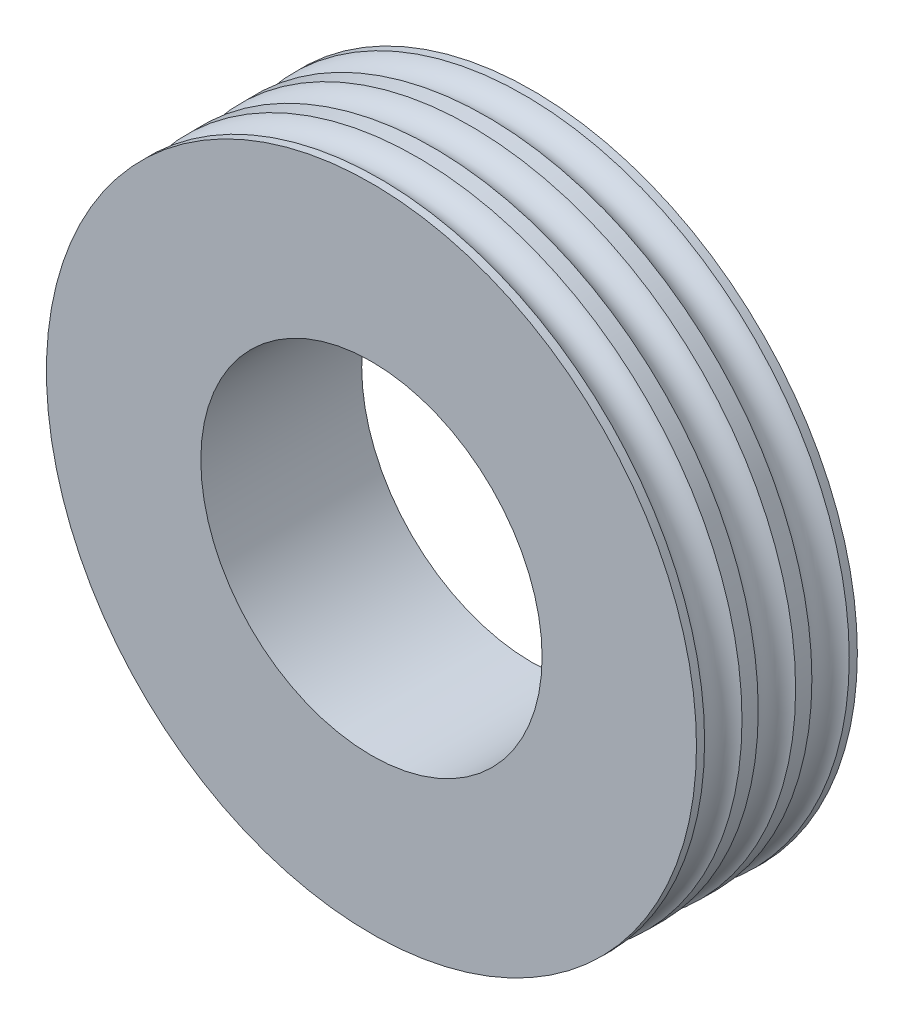
SolidWorks part; units mm, degrees
ref_plane "Front Plane" through (0, 0, 0) normal (0, 0, 1) x (1, 0, 0)
ref_plane "Top Plane" through (0, 0, 0) normal (0, 1, 0) x (1, 0, 0)
ref_plane "Right Plane" through (0, 0, 0) normal (1, 0, 0) x (0, 0, -1)
sketch "Sketch2" plane through (0, 0, 0) normal (1, 0, 0) x (0, 0, -1)
  line L0 (-0.34, 2.1) -> (-0.34, 4)
  line L1 (-0.34, 4) -> (-0.44, 4)
  line L2 (-1, 4) -> (-1, 2.1)
  line L4 (-1, 2.1) -> (-0.34, 2.1)
  line L5 (-3.0147, 0) -> (3.0268, 0) construction
  line L6 (-0.9, 4) -> (-1, 4)
  arc A0 (-0.9, 4) -> (-0.44, 4) centre (-0.67, 4.1) ccw
  dimension "D6" = 0.1
  dimension "D1" = 2.1
  dimension "D2" = 0.66
  dimension "D3" = 4
  dimension "D4" = 0.1
  dimension "D5" = 0.1
revolve "Revolve1" add sketch "Sketch2" angle 360 about L5
ref_plane "Plane1" through (0, 0, 0.34) normal (0, 0, -1) x (-1, 0, 0)
mirror "Mirror2" about plane through (0, 0, 0.34) normal (0, 0, -1) of "Revolve1"
ref_plane "Plane3" through (0, 0, 1) normal (0, 0, 1) x (1, 0, 0)
mirror "Mirror3" about plane through (0, 0, 1) normal (0, 0, 1) of "Revolve1"
